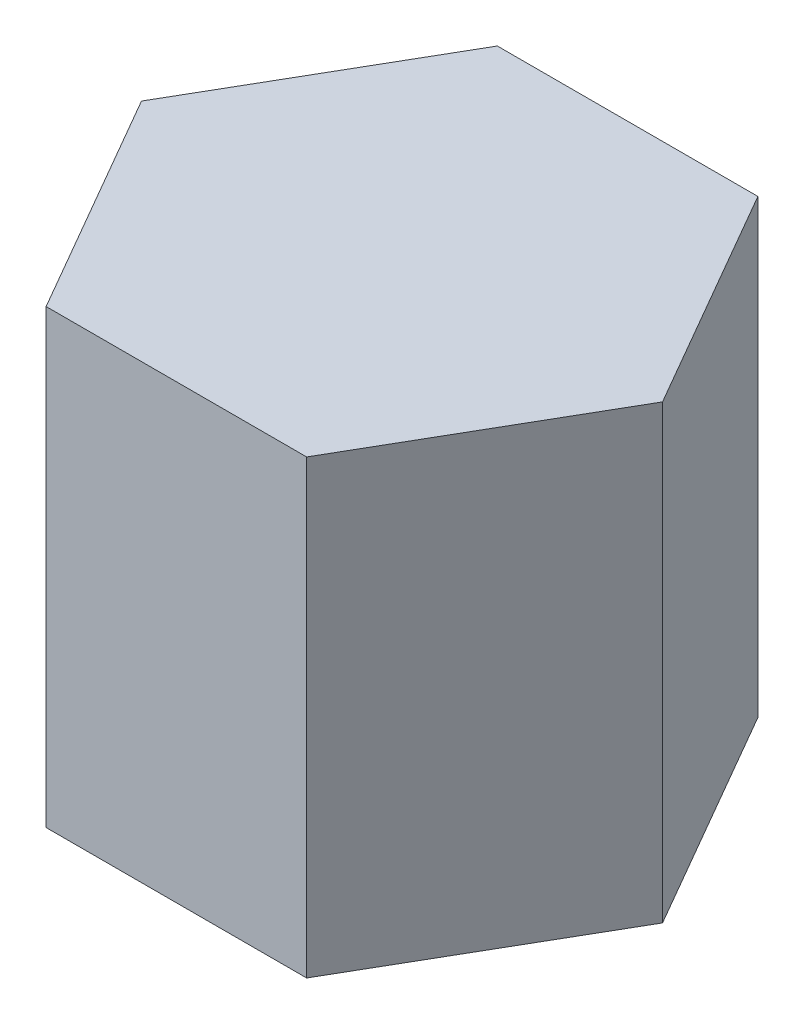
SolidWorks part; units mm, degrees
ref_plane "Front" through (0, 0, 0) normal (0, 0, 1) x (1, 0, 0)
ref_plane "Top" through (0, 0, 0) normal (0, 1, 0) x (1, 0, 0)
ref_plane "Right" through (0, 0, 0) normal (1, 0, 0) x (0, 0, -1)
sketch "草圖1" plane through (0, 0, 0) normal (0, 1, 0) x (1, 0, 0)
  line L1 (28.8675, 0) -> (14.4338, 25)
  line L2 (14.4338, 25) -> (-14.4338, 25)
  line L3 (-14.4338, 25) -> (-28.8675, 0)
  line L4 (-28.8675, 0) -> (-14.4338, -25)
  line L5 (-14.4338, -25) -> (14.4338, -25)
  line L6 (14.4338, -25) -> (28.8675, 0)
  circle A0 centre (0, 0) radius 25 construction
  dimension "D1" = 50
extrude "填料-伸長1" add sketch "草圖1" along normal blind 50
